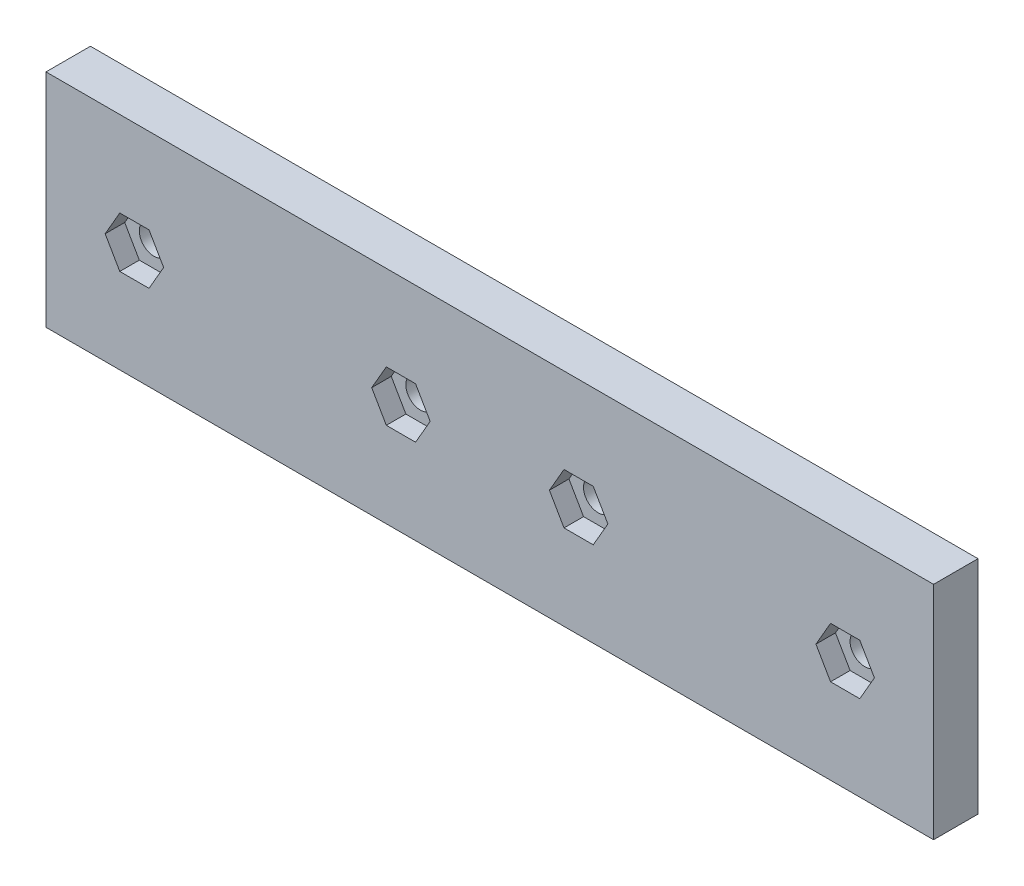
SolidWorks part; units mm, degrees
ref_plane "Front Plane" through (0, 0, 0) normal (0, 0, 1) x (1, 0, 0)
ref_plane "Top Plane" through (0, 0, 0) normal (0, 1, 0) x (1, 0, 0)
ref_plane "Right Plane" through (0, 0, 0) normal (1, 0, 0) x (0, 0, -1)
sketch "Sketch1" plane through (0, 0, -70.6794) normal (0, 0, 1) x (1, 0, 0)
  line L0 (22.4738, -921.0784) -> (22.4738, 49078.9216) construction
  line L1 (22.4738, 66.4216) -> (22.4738, 91.4216) construction
  line L2 (-977.5262, 78.9216) -> (49022.4738, 78.9216) construction
  line L3 (-27.5262, 91.4216) -> (-27.5262, 66.4216) construction
  line L4 (-27.4762, 91.3716) -> (72.4238, 91.3716)
  line L5 (-27.4762, 91.3716) -> (-27.4762, 66.4716)
  line L6 (-27.4762, 66.4716) -> (72.4238, 66.4716)
  line L7 (72.4238, 91.3716) -> (72.4238, 66.4716)
  line L8 (22.4738, 91.4216) -> (72.4738, 91.4216) construction
  circle A0 centre (-17.5262, 78.9216) radius 1.65
  circle A1 centre (12.4738, 78.9216) radius 1.65
  circle A2 centre (32.4738, 78.9216) radius 1.65
  circle A3 centre (62.4738, 78.9216) radius 1.65
  circle A4 centre (-17.5262, 78.9216) radius 1.65 construction
  point P5 (22.4738, 78.9216)
  dimension "D1" = 0.05
  dimension "D2" = 0.05
extrude "Boss-Extrude1" add sketch "Sketch1" along normal blind 5
sketch "Sketch2" plane through (0, 0, -65.6794) normal (0, 0, 1) x (1, 0, 0)
  line L1 (-15.8807, 76.0716) -> (-14.2353, 78.9216)
  line L2 (-14.2353, 78.9216) -> (-15.8807, 81.7716)
  line L3 (-15.8807, 81.7716) -> (-19.1716, 81.7716)
  line L4 (-19.1716, 81.7716) -> (-20.8171, 78.9216)
  line L5 (-20.8171, 78.9216) -> (-19.1716, 76.0716)
  line L6 (-19.1716, 76.0716) -> (-15.8807, 76.0716)
  line L7 (14.1193, 76.0716) -> (15.7647, 78.9216)
  line L8 (15.7647, 78.9216) -> (14.1193, 81.7716)
  line L9 (14.1193, 81.7716) -> (10.8284, 81.7716)
  line L10 (10.8284, 81.7716) -> (9.1829, 78.9216)
  line L11 (9.1829, 78.9216) -> (10.8284, 76.0716)
  line L12 (10.8284, 76.0716) -> (14.1193, 76.0716)
  line L13 (34.1193, 76.0716) -> (35.7647, 78.9216)
  line L14 (35.7647, 78.9216) -> (34.1193, 81.7716)
  line L15 (34.1193, 81.7716) -> (30.8284, 81.7716)
  line L16 (30.8284, 81.7716) -> (29.1829, 78.9216)
  line L17 (29.1829, 78.9216) -> (30.8284, 76.0716)
  line L18 (30.8284, 76.0716) -> (34.1193, 76.0716)
  line L19 (64.1193, 76.0716) -> (65.7647, 78.9216)
  line L20 (65.7647, 78.9216) -> (64.1193, 81.7716)
  line L21 (64.1193, 81.7716) -> (60.8284, 81.7716)
  line L22 (60.8284, 81.7716) -> (59.1829, 78.9216)
  line L23 (59.1829, 78.9216) -> (60.8284, 76.0716)
  line L24 (60.8284, 76.0716) -> (64.1193, 76.0716)
  circle A0 centre (-17.5262, 78.9216) radius 2.85 construction
  circle A1 centre (12.4738, 78.9216) radius 2.85 construction
  circle A2 centre (32.4738, 78.9216) radius 2.85 construction
  circle A3 centre (62.4738, 78.9216) radius 2.85 construction
  dimension "D1" = 5.7
extrude "Cut-Extrude1" cut sketch "Sketch2" against normal blind 2.2
